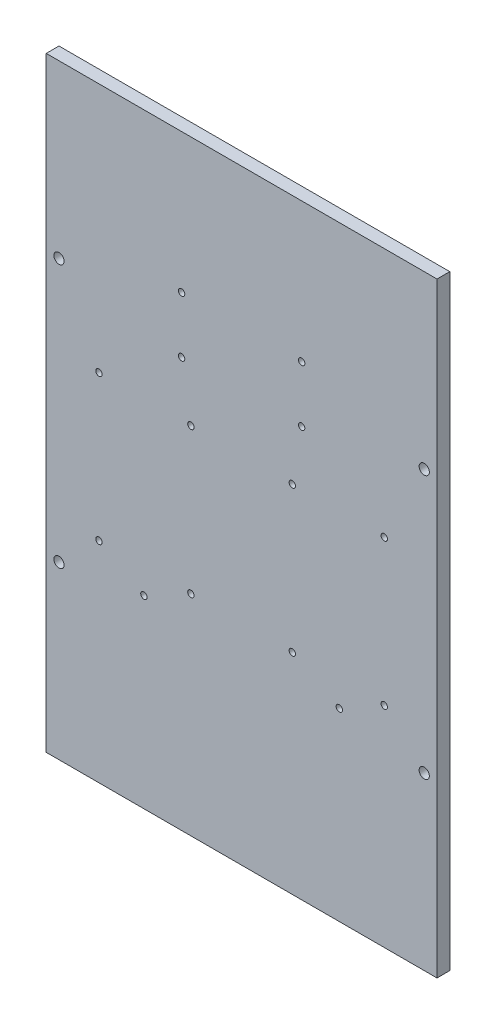
SolidWorks part; units mm, degrees
ref_plane "Alzado" through (0, 0, 0) normal (0, 0, 1) x (1, 0, 0)
ref_plane "Planta" through (0, 0, 0) normal (0, 1, 0) x (1, 0, 0)
ref_plane "Vista lateral" through (0, 0, 0) normal (1, 0, 0) x (0, 0, -1)
sketch "Croquis1" plane through (0, 0, 0) normal (0, 0, 1) x (1, 0, 0)
  line L1 (0, 0) -> (153, 0)
  line L2 (0, 0) -> (0, 237)
  line L3 (0, 237) -> (153, 237)
  line L4 (153, 0) -> (153, 237)
  dimension "D1" = 153
  dimension "D2" = 237
extrude "Saliente-Extruir1" add sketch "Croquis1" along normal blind 5
sketch "Croquis2" plane through (0, 0, 5) normal (0, 0, 1) x (1, 0, 0)
  line L0 (0, 118.5) -> (153, 118.5) construction
  line L1 (0, 237) -> (0, 0) construction
  line L2 (153, 0) -> (153, 237) construction
  line L3 (0, 146.4427) -> (5, 146.4427) construction
  line L4 (5, 118.5) -> (5, 170) construction
  line L5 (76.5, 237) -> (76.5, 0) construction
  line L6 (153, 237) -> (0, 237) construction
  line L7 (0, 0) -> (153, 0) construction
  circle A0 centre (5, 170) radius 2
  circle A1 centre (148, 170) radius 2
  circle A2 centre (5, 67) radius 2
  circle A3 centre (148, 67) radius 2
  dimension "D1" = 51.5
  dimension "D2" = 51.5
  dimension "D3" = 5
extrude "Cortar-Extruir1" cut sketch "Croquis2" against normal blind 5
sketch "Croquis3" plane through (0, 0, 5) normal (0, 0, 1) x (1, 0, 0)
  line L0 (76.5, 237) -> (76.5, 0) construction
  line L1 (153, 237) -> (0, 237) construction
  line L2 (0, 0) -> (153, 0) construction
  line L3 (76.5, 0) -> (76.5, 5) construction
  line L4 (76.5, 0) -> (76.5, 25) construction
  line L5 (76.5, 0) -> (82.5, 0) construction
  line L10 (82.5, 0) -> (82.5, 25) construction
  line L11 (82.5, 25) -> (82.5, 71) construction
  line L12 (38.6493, 110.5901) -> (38.6493, 142.0901) construction
  line L21 (16.1493, 142.0901) -> (61.1493, 142.0901) construction
  line L22 (16.1493, 142.0901) -> (16.1493, 79.0901) construction
  line L23 (16.1493, 79.0901) -> (61.1493, 79.0901) construction
  line L24 (61.1493, 142.0901) -> (61.1493, 79.0901) construction
  line L25 (16.1493, 142.0901) -> (61.1493, 79.0901) construction
  line L26 (16.1493, 79.0901) -> (61.1493, 142.0901) construction
  line L27 (38.6493, 142.0901) -> (20.6493, 142.0901) construction
  line L28 (153, 0) -> (76.5, 0) construction
  line L29 (38.6493, 110.5901) -> (16.1493, 110.5901) construction
  line L30 (20.6493, 194.8792) -> (20.6493, 139.0901) construction
  line L31 (76.5, 0) -> (114.75, 0) construction
  line L32 (114.75, 0) -> (114.75, 114.051) construction
  circle A0 centre (20.6493, 139.0901) radius 1.25
  circle A1 centre (56.6493, 139.0901) radius 1.25
  circle A2 centre (56.6493, 82.0901) radius 1.25
  circle A3 centre (20.6493, 82.0901) radius 1.25
  circle A4 centre (114.75, 72.3023) radius 1.25
  circle A5 centre (38.25, 72.3023) radius 1.25
  circle A6 centre (132.3507, 82.0901) radius 1.25
  circle A7 centre (96.3507, 82.0901) radius 1.25
  circle A8 centre (96.3507, 139.0901) radius 1.25
  circle A9 centre (132.3507, 139.0901) radius 1.25
  point P22 (38.6493, 110.5901)
  dimension "D3" = 57
  dimension "D4" = 36
  dimension "D5" = 2.5
  dimension "D1" = 46
  dimension "D2" = 25
  dimension "D6" = 45
  dimension "D7" = 63
extrude "Cortar-Extruir2" cut sketch "Croquis3" against normal blind 10
sketch "Croquis4" plane through (0, 0, 5) normal (0, 0, 1) x (1, 0, 0)
  line L0 (76.5, 237) -> (76.5, 0) construction
  line L1 (53, 160.4588) -> (100, 160.4588) construction
  line L2 (53, 160.4588) -> (53, 182.4588) construction
  line L3 (53, 182.4588) -> (100, 182.4588) construction
  line L4 (100, 160.4588) -> (100, 182.4588) construction
  line L5 (153, 237) -> (0, 237) construction
  line L6 (0, 0) -> (153, 0) construction
  line L7 (76.5, 182.4588) -> (76.5, 160.4588) construction
  circle A0 centre (53, 182.4588) radius 1.25
  circle A1 centre (53, 160.4588) radius 1.25
  circle A2 centre (100, 182.4588) radius 1.25
  circle A3 centre (100, 160.4588) radius 1.25
  dimension "D1" = 22
  dimension "D2" = 47
extrude "Cortar-Extruir3" cut sketch "Croquis4" against normal blind 10
sketch "Croquis5" plane through (0, 0, 5) normal (0, 0, 1) x (1, 0, 0)
  line L0 (76.5, 237) -> (76.5, 0) construction
  line L1 (153, 237) -> (0, 237) construction
  line L2 (0, 0) -> (153, 0) construction
  line L3 (0, 118.5) -> (153, 118.5) construction
  line L4 (0, 237) -> (0, 0) construction
  line L5 (153, 0) -> (153, 237) construction
  line L7 (-6, 237) -> (159, 237) construction
  line L8 (-6, 237) -> (-6, 0) construction
  line L9 (-6, 0) -> (159, 0) construction
  line L10 (159, 237) -> (159, 0) construction
  line L11 (-6, 237) -> (159, 0) construction
  line L12 (-6, 0) -> (159, 237) construction
  circle A0 centre (148, 170) radius 2 construction
  point P12 (76.5, 118.5)
  point P13 (76.5, 118.5)
  point P21 (148, 169.8496)
  dimension "D2" = 11
  dimension "D3" = 5
  dimension "D1" = 165
